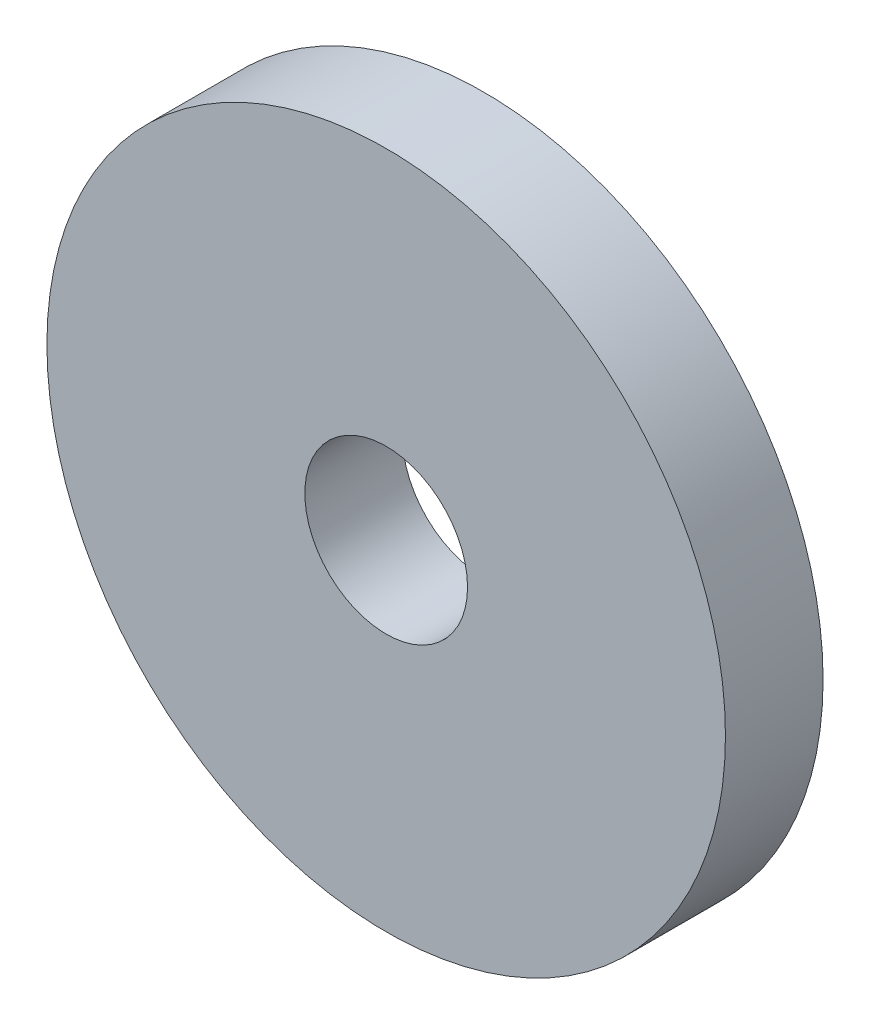
SolidWorks part; units mm, degrees
ref_plane "Front Plane" through (0, 0, 0) normal (0, 0, 1) x (1, 0, 0)
ref_plane "Top Plane" through (0, 0, 0) normal (0, 1, 0) x (1, 0, 0)
ref_plane "Right Plane" through (0, 0, 0) normal (1, 0, 0) x (0, 0, -1)
sketch "Sketch1" plane through (0, 0, 0) normal (0, 0, 1) x (1, 0, 0)
  circle A0 centre (0, 0) radius 104.25
  circle A1 centre (0, 0) radius 25
extrude "Boss-Extrude1" add sketch "Sketch1" along normal blind 30
